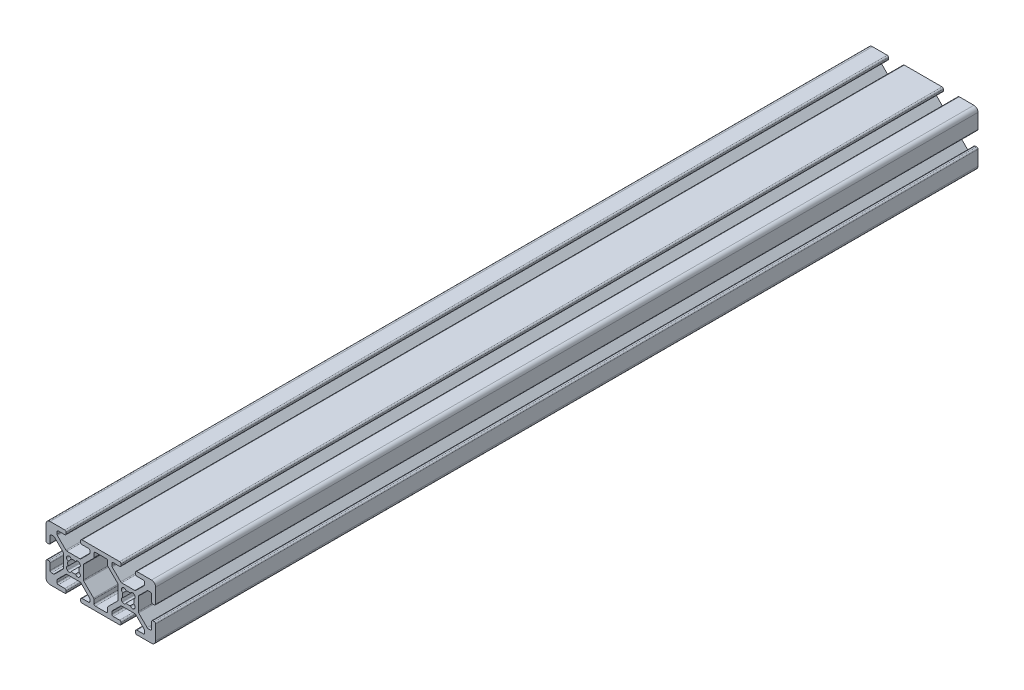
SolidWorks part; units mm, degrees
material "6105-T5 Aluminum"
ref_plane "Front Plane" through (0, 0, 0) normal (0, 0, 1) x (1, 0, 0)
ref_plane "Top Plane" through (0, 0, 0) normal (0, 1, 0) x (1, 0, 0)
ref_plane "Right Plane" through (0, 0, 0) normal (1, 0, 0) x (0, 0, -1)
sketch "Sketch1" plane through (0, 0, 0) normal (0, 0, 1) x (1, 0, 0)
  line L0 (-2.1249, -2.3045) -> (-2.3045, -2.1249)
  line L1 (-2.3045, 2.1249) -> (-2.1249, 2.3045)
  line L2 (2.1249, 2.3045) -> (2.3045, 2.1249)
  line L3 (2.3045, -2.1249) -> (2.1249, -2.3045)
  line L4 (-12.505, -7.992) -> (-12.505, -6.6448)
  line L5 (-12.6538, -6.2856) -> (-16.1962, -2.7431)
  line L6 (-16.345, -2.3839) -> (-16.345, 2.3839)
  line L7 (-16.1962, 2.7431) -> (-12.6538, 6.2856)
  line L8 (-12.505, 6.6448) -> (-12.505, 7.992)
  line L9 (-11.997, 8.5) -> (-8.003, 8.5)
  line L10 (-7.495, 7.992) -> (-7.495, 6.6448)
  line L11 (-7.3462, 6.2856) -> (-3.8038, 2.7431)
  line L12 (-3.655, 2.3839) -> (-3.655, -2.3839)
  line L13 (-3.8038, -2.7431) -> (-7.3462, -6.2856)
  line L14 (-7.495, -6.6448) -> (-7.495, -7.992)
  line L15 (-8.003, -8.5) -> (-11.997, -8.5)
  line L16 (-22.1249, -2.3045) -> (-22.3045, -2.1249)
  line L17 (-22.3045, 2.1249) -> (-22.1249, 2.3045)
  line L18 (-17.8751, 2.3045) -> (-17.6955, 2.1249)
  line L19 (-17.6955, -2.1249) -> (-17.8751, -2.3045)
  line L20 (-22.3839, -3.655) -> (-17.6161, -3.655)
  line L21 (-17.2569, -3.8038) -> (-14.1538, -6.9069)
  line L22 (-14.005, -7.2661) -> (-14.005, -7.992)
  line L23 (-14.513, -8.5) -> (-16.862, -8.5)
  line L24 (-17.37, -9.008) -> (-17.37, -9.492)
  line L25 (-16.862, -10) -> (-3.138, -10)
  line L26 (-2.63, -9.492) -> (-2.63, -9.008)
  line L27 (-3.138, -8.5) -> (-5.487, -8.5)
  line L28 (-5.995, -7.992) -> (-5.995, -7.2661)
  line L29 (-5.8462, -6.9069) -> (-2.7431, -3.8038)
  line L30 (-2.3839, -3.655) -> (2.3839, -3.655)
  line L31 (2.7431, -3.8038) -> (5.8462, -6.9069)
  line L32 (5.995, -7.2661) -> (5.995, -7.992)
  line L33 (5.487, -8.5) -> (3.138, -8.5)
  line L34 (2.63, -9.008) -> (2.63, -9.492)
  line L35 (3.138, -10) -> (8.5, -10)
  line L36 (10, -8.5) -> (10, -3.138)
  line L37 (9.492, -2.63) -> (9.008, -2.63)
  line L38 (8.5, -3.138) -> (8.5, -5.487)
  line L39 (7.992, -5.995) -> (7.2661, -5.995)
  line L40 (6.9069, -5.8462) -> (3.8038, -2.7431)
  line L41 (3.655, -2.3839) -> (3.655, 2.3839)
  line L42 (3.8038, 2.7431) -> (6.9069, 5.8462)
  line L43 (7.2661, 5.995) -> (7.992, 5.995)
  line L44 (8.5, 5.487) -> (8.5, 3.138)
  line L45 (9.008, 2.63) -> (9.492, 2.63)
  line L46 (10, 3.138) -> (10, 8.5)
  line L47 (8.5, 10) -> (3.138, 10)
  line L48 (2.63, 9.492) -> (2.63, 9.008)
  line L49 (3.138, 8.5) -> (5.487, 8.5)
  line L50 (5.995, 7.992) -> (5.995, 7.2661)
  line L51 (5.8462, 6.9069) -> (2.7431, 3.8038)
  line L52 (2.3839, 3.655) -> (-2.3839, 3.655)
  line L53 (-2.7431, 3.8038) -> (-5.8462, 6.9069)
  line L54 (-5.995, 7.2661) -> (-5.995, 7.992)
  line L55 (-5.487, 8.5) -> (-3.138, 8.5)
  line L56 (-2.63, 9.008) -> (-2.63, 9.492)
  line L57 (-3.138, 10) -> (-16.862, 10)
  line L58 (-17.37, 9.492) -> (-17.37, 9.008)
  line L59 (-16.862, 8.5) -> (-14.513, 8.5)
  line L60 (-14.005, 7.992) -> (-14.005, 7.2661)
  line L61 (-14.1538, 6.9069) -> (-17.2569, 3.8038)
  line L62 (-17.6161, 3.655) -> (-22.3839, 3.655)
  line L63 (-22.7431, 3.8038) -> (-25.8462, 6.9069)
  line L64 (-25.995, 7.2661) -> (-25.995, 7.992)
  line L65 (-25.487, 8.5) -> (-23.138, 8.5)
  line L66 (-22.63, 9.008) -> (-22.63, 9.492)
  line L67 (-23.138, 10) -> (-28.5, 10)
  line L68 (-30, 8.5) -> (-30, 3.138)
  line L69 (-29.492, 2.63) -> (-29.008, 2.63)
  line L70 (-28.5, 3.138) -> (-28.5, 5.487)
  line L71 (-27.992, 5.995) -> (-27.2661, 5.995)
  line L72 (-26.9069, 5.8462) -> (-23.8038, 2.7431)
  line L73 (-23.655, 2.3839) -> (-23.655, -2.3839)
  line L74 (-23.8038, -2.7431) -> (-26.9069, -5.8462)
  line L75 (-27.2661, -5.995) -> (-27.992, -5.995)
  line L76 (-28.5, -5.487) -> (-28.5, -3.138)
  line L77 (-29.008, -2.63) -> (-29.492, -2.63)
  line L78 (-30, -3.138) -> (-30, -8.5)
  line L79 (-28.5, -10) -> (-23.138, -10)
  line L80 (-22.63, -9.492) -> (-22.63, -9.008)
  line L81 (-23.138, -8.5) -> (-25.487, -8.5)
  line L82 (-25.995, -7.992) -> (-25.995, -7.2661)
  line L83 (-25.8462, -6.9069) -> (-22.7431, -3.8038)
  arc A0 (-1.9351, -0.804) -> (-2.3045, -2.1249) centre (-1.748, -1.5684) ccw
  arc A1 (-1.9351, 0.804) -> (-1.9351, -0.804) centre (0, 0) ccw
  arc A2 (-2.3045, 2.1249) -> (-1.9351, 0.804) centre (-1.748, 1.5684) ccw
  arc A3 (-0.804, 1.9351) -> (-2.1249, 2.3045) centre (-1.5684, 1.748) ccw
  arc A4 (0.804, 1.9351) -> (-0.804, 1.9351) centre (0, 0) ccw
  arc A5 (2.1249, 2.3045) -> (0.804, 1.9351) centre (1.5684, 1.748) ccw
  arc A6 (1.9351, 0.804) -> (2.3045, 2.1249) centre (1.748, 1.5684) ccw
  arc A7 (1.9351, -0.804) -> (1.9351, 0.804) centre (0, 0) ccw
  arc A8 (2.3045, -2.1249) -> (1.9351, -0.804) centre (1.748, -1.5684) ccw
  arc A9 (0.804, -1.9351) -> (2.1249, -2.3045) centre (1.5684, -1.748) ccw
  arc A10 (-0.804, -1.9351) -> (0.804, -1.9351) centre (0, 0) ccw
  arc A11 (-2.1249, -2.3045) -> (-0.804, -1.9351) centre (-1.5684, -1.748) ccw
  arc A12 (-12.505, -7.992) -> (-11.997, -8.5) centre (-11.997, -7.992) ccw
  arc A13 (-12.505, -6.6448) -> (-12.6538, -6.2856) centre (-13.013, -6.6448) ccw
  arc A14 (-16.345, -2.3839) -> (-16.1962, -2.7431) centre (-15.837, -2.3839) ccw
  arc A15 (-16.1962, 2.7431) -> (-16.345, 2.3839) centre (-15.837, 2.3839) ccw
  arc A16 (-12.6538, 6.2856) -> (-12.505, 6.6448) centre (-13.013, 6.6448) ccw
  arc A17 (-11.997, 8.5) -> (-12.505, 7.992) centre (-11.997, 7.992) ccw
  arc A18 (-7.495, 7.992) -> (-8.003, 8.5) centre (-8.003, 7.992) ccw
  arc A19 (-7.495, 6.6448) -> (-7.3462, 6.2856) centre (-6.987, 6.6448) ccw
  arc A20 (-3.655, 2.3839) -> (-3.8038, 2.7431) centre (-4.163, 2.3839) ccw
  arc A21 (-3.8038, -2.7431) -> (-3.655, -2.3839) centre (-4.163, -2.3839) ccw
  arc A22 (-7.3462, -6.2856) -> (-7.495, -6.6448) centre (-6.987, -6.6448) ccw
  arc A23 (-8.003, -8.5) -> (-7.495, -7.992) centre (-8.003, -7.992) ccw
  arc A24 (-21.9351, -0.804) -> (-22.3045, -2.1249) centre (-21.748, -1.5684) ccw
  arc A25 (-21.9351, 0.804) -> (-21.9351, -0.804) centre (-20, 0) ccw
  arc A26 (-22.3045, 2.1249) -> (-21.9351, 0.804) centre (-21.748, 1.5684) ccw
  arc A27 (-20.804, 1.9351) -> (-22.1249, 2.3045) centre (-21.5684, 1.748) ccw
  arc A28 (-19.196, 1.9351) -> (-20.804, 1.9351) centre (-20, 0) ccw
  arc A29 (-17.8751, 2.3045) -> (-19.196, 1.9351) centre (-18.4316, 1.748) ccw
  arc A30 (-18.0649, 0.804) -> (-17.6955, 2.1249) centre (-18.252, 1.5684) ccw
  arc A31 (-18.0649, -0.804) -> (-18.0649, 0.804) centre (-20, 0) ccw
  arc A32 (-17.6955, -2.1249) -> (-18.0649, -0.804) centre (-18.252, -1.5684) ccw
  arc A33 (-19.196, -1.9351) -> (-17.8751, -2.3045) centre (-18.4316, -1.748) ccw
  arc A34 (-20.804, -1.9351) -> (-19.196, -1.9351) centre (-20, 0) ccw
  arc A35 (-22.1249, -2.3045) -> (-20.804, -1.9351) centre (-21.5684, -1.748) ccw
  arc A36 (-22.3839, -3.655) -> (-22.7431, -3.8038) centre (-22.3839, -4.163) ccw
  arc A37 (-17.2569, -3.8038) -> (-17.6161, -3.655) centre (-17.6161, -4.163) ccw
  arc A38 (-14.005, -7.2661) -> (-14.1538, -6.9069) centre (-14.513, -7.2661) ccw
  arc A39 (-14.513, -8.5) -> (-14.005, -7.992) centre (-14.513, -7.992) ccw
  arc A40 (-16.862, -8.5) -> (-17.37, -9.008) centre (-16.862, -9.008) ccw
  arc A41 (-17.37, -9.492) -> (-16.862, -10) centre (-16.862, -9.492) ccw
  arc A42 (-3.138, -10) -> (-2.63, -9.492) centre (-3.138, -9.492) ccw
  arc A43 (-2.63, -9.008) -> (-3.138, -8.5) centre (-3.138, -9.008) ccw
  arc A44 (-5.995, -7.992) -> (-5.487, -8.5) centre (-5.487, -7.992) ccw
  arc A45 (-5.8462, -6.9069) -> (-5.995, -7.2661) centre (-5.487, -7.2661) ccw
  arc A46 (-2.3839, -3.655) -> (-2.7431, -3.8038) centre (-2.3839, -4.163) ccw
  arc A47 (2.7431, -3.8038) -> (2.3839, -3.655) centre (2.3839, -4.163) ccw
  arc A48 (5.995, -7.2661) -> (5.8462, -6.9069) centre (5.487, -7.2661) ccw
  arc A49 (5.487, -8.5) -> (5.995, -7.992) centre (5.487, -7.992) ccw
  arc A50 (3.138, -8.5) -> (2.63, -9.008) centre (3.138, -9.008) ccw
  arc A51 (2.63, -9.492) -> (3.138, -10) centre (3.138, -9.492) ccw
  arc A52 (8.5, -10) -> (10, -8.5) centre (8.5, -8.5) ccw
  arc A53 (10, -3.138) -> (9.492, -2.63) centre (9.492, -3.138) ccw
  arc A54 (9.008, -2.63) -> (8.5, -3.138) centre (9.008, -3.138) ccw
  arc A55 (7.992, -5.995) -> (8.5, -5.487) centre (7.992, -5.487) ccw
  arc A56 (6.9069, -5.8462) -> (7.2661, -5.995) centre (7.2661, -5.487) ccw
  arc A57 (3.655, -2.3839) -> (3.8038, -2.7431) centre (4.163, -2.3839) ccw
  arc A58 (3.8038, 2.7431) -> (3.655, 2.3839) centre (4.163, 2.3839) ccw
  arc A59 (7.2661, 5.995) -> (6.9069, 5.8462) centre (7.2661, 5.487) ccw
  arc A60 (8.5, 5.487) -> (7.992, 5.995) centre (7.992, 5.487) ccw
  arc A61 (8.5, 3.138) -> (9.008, 2.63) centre (9.008, 3.138) ccw
  arc A62 (9.492, 2.63) -> (10, 3.138) centre (9.492, 3.138) ccw
  arc A63 (10, 8.5) -> (8.5, 10) centre (8.5, 8.5) ccw
  arc A64 (3.138, 10) -> (2.63, 9.492) centre (3.138, 9.492) ccw
  arc A65 (2.63, 9.008) -> (3.138, 8.5) centre (3.138, 9.008) ccw
  arc A66 (5.995, 7.992) -> (5.487, 8.5) centre (5.487, 7.992) ccw
  arc A67 (5.8462, 6.9069) -> (5.995, 7.2661) centre (5.487, 7.2661) ccw
  arc A68 (2.3839, 3.655) -> (2.7431, 3.8038) centre (2.3839, 4.163) ccw
  arc A69 (-2.7431, 3.8038) -> (-2.3839, 3.655) centre (-2.3839, 4.163) ccw
  arc A70 (-5.995, 7.2661) -> (-5.8462, 6.9069) centre (-5.487, 7.2661) ccw
  arc A71 (-5.487, 8.5) -> (-5.995, 7.992) centre (-5.487, 7.992) ccw
  arc A72 (-3.138, 8.5) -> (-2.63, 9.008) centre (-3.138, 9.008) ccw
  arc A73 (-2.63, 9.492) -> (-3.138, 10) centre (-3.138, 9.492) ccw
  arc A74 (-16.862, 10) -> (-17.37, 9.492) centre (-16.862, 9.492) ccw
  arc A75 (-17.37, 9.008) -> (-16.862, 8.5) centre (-16.862, 9.008) ccw
  arc A76 (-14.005, 7.992) -> (-14.513, 8.5) centre (-14.513, 7.992) ccw
  arc A77 (-14.1538, 6.9069) -> (-14.005, 7.2661) centre (-14.513, 7.2661) ccw
  arc A78 (-17.6161, 3.655) -> (-17.2569, 3.8038) centre (-17.6161, 4.163) ccw
  arc A79 (-22.7431, 3.8038) -> (-22.3839, 3.655) centre (-22.3839, 4.163) ccw
  arc A80 (-25.995, 7.2661) -> (-25.8462, 6.9069) centre (-25.487, 7.2661) ccw
  arc A81 (-25.487, 8.5) -> (-25.995, 7.992) centre (-25.487, 7.992) ccw
  arc A82 (-23.138, 8.5) -> (-22.63, 9.008) centre (-23.138, 9.008) ccw
  arc A83 (-22.63, 9.492) -> (-23.138, 10) centre (-23.138, 9.492) ccw
  arc A84 (-28.5, 10) -> (-30, 8.5) centre (-28.5, 8.5) ccw
  arc A85 (-30, 3.138) -> (-29.492, 2.63) centre (-29.492, 3.138) ccw
  arc A86 (-29.008, 2.63) -> (-28.5, 3.138) centre (-29.008, 3.138) ccw
  arc A87 (-27.992, 5.995) -> (-28.5, 5.487) centre (-27.992, 5.487) ccw
  arc A88 (-26.9069, 5.8462) -> (-27.2661, 5.995) centre (-27.2661, 5.487) ccw
  arc A89 (-23.655, 2.3839) -> (-23.8038, 2.7431) centre (-24.163, 2.3839) ccw
  arc A90 (-23.8038, -2.7431) -> (-23.655, -2.3839) centre (-24.163, -2.3839) ccw
  arc A91 (-27.2661, -5.995) -> (-26.9069, -5.8462) centre (-27.2661, -5.487) ccw
  arc A92 (-28.5, -5.487) -> (-27.992, -5.995) centre (-27.992, -5.487) ccw
  arc A93 (-28.5, -3.138) -> (-29.008, -2.63) centre (-29.008, -3.138) ccw
  arc A94 (-29.492, -2.63) -> (-30, -3.138) centre (-29.492, -3.138) ccw
  arc A95 (-30, -8.5) -> (-28.5, -10) centre (-28.5, -8.5) ccw
  arc A96 (-23.138, -10) -> (-22.63, -9.492) centre (-23.138, -9.492) ccw
  arc A97 (-22.63, -9.008) -> (-23.138, -8.5) centre (-23.138, -9.008) ccw
  arc A98 (-25.995, -7.992) -> (-25.487, -8.5) centre (-25.487, -7.992) ccw
  arc A99 (-25.8462, -6.9069) -> (-25.995, -7.2661) centre (-25.487, -7.2661) ccw
extrude "Extrude1" add sketch "Sketch1" against normal blind 300
